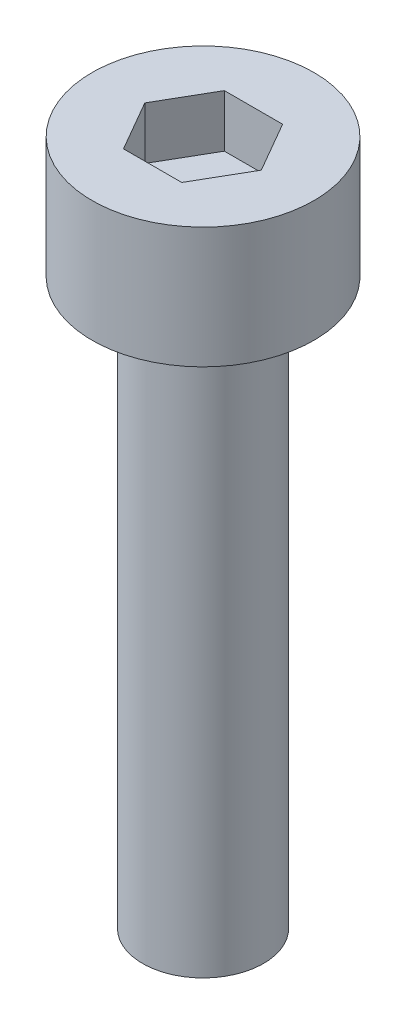
SolidWorks part; units mm, degrees
material "Plain Carbon Steel"
ref_plane "Front Plane" through (0, 0, 0) normal (0, 0, 1) x (1, 0, 0)
ref_plane "Top Plane" through (0, 0, 0) normal (0, 1, 0) x (1, 0, 0)
ref_plane "Right Plane" through (0, 0, 0) normal (1, 0, 0) x (0, 0, -1)
sketch "Sketch1" plane through (0, 0, 0) normal (0, 0, 1) x (1, 0, 0)
  line L0 (0, 0) -> (0, 49.351) construction
  line L1 (0, 17) -> (2.75, 17)
  line L2 (2.75, 17) -> (2.75, 14)
  line L3 (2.75, 14) -> (1.5, 14)
  line L4 (1.5, 14) -> (1.5, 0)
  line L5 (1.5, 0) -> (0, 0)
  line L6 (0, 0) -> (0, 17)
  dimension "D1" = 14
  dimension "D2" = 5.5
  dimension "D3" = 3
  dimension "D4" = 3
revolve "Revolve1" add sketch "Sketch1" angle 360 about L0
sketch "Sketch2" plane through (0, 17, 0) normal (0, 1, 0) x (1, 0, 0)
  line L1 (-0.7217, 1.25) -> (-1.4434, 0)
  line L2 (-1.4434, 0) -> (-0.7217, -1.25)
  line L3 (-0.7217, -1.25) -> (0.7217, -1.25)
  line L4 (0.7217, -1.25) -> (1.4434, 0)
  line L5 (1.4434, 0) -> (0.7217, 1.25)
  line L6 (0.7217, 1.25) -> (-0.7217, 1.25)
  circle A0 centre (0, 0) radius 1.25 construction
  dimension "D1" = 2.5
extrude "Cut-Extrude1" cut sketch "Sketch2" against normal blind 1.3
